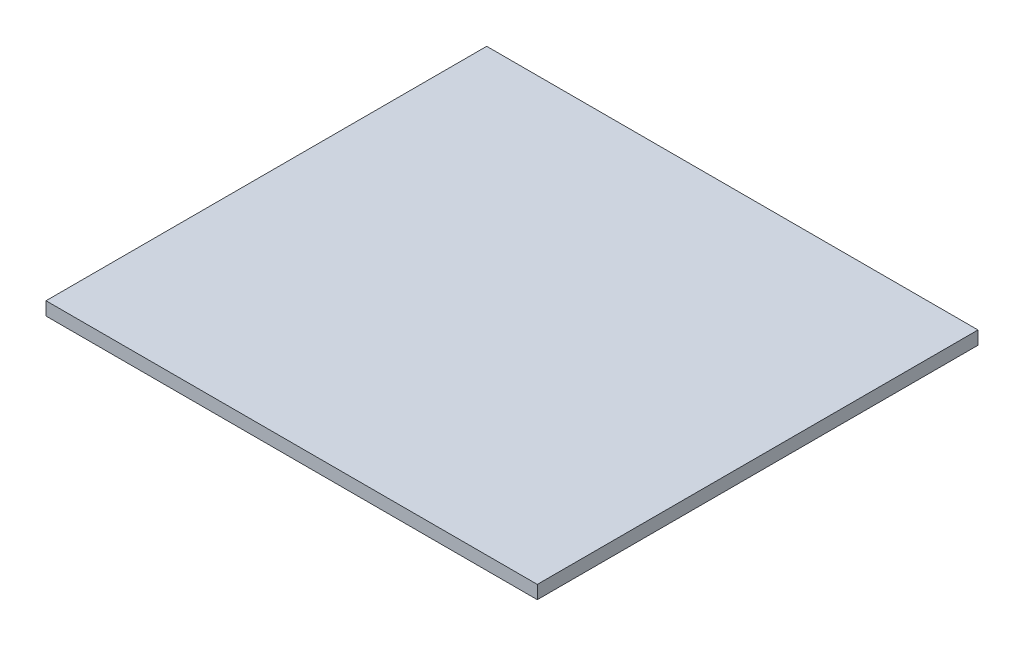
SolidWorks part; units mm, degrees
ref_plane "Front" through (0, 0, 0) normal (0, 0, 1) x (1, 0, 0)
ref_plane "Top" through (0, 0, 0) normal (0, 1, 0) x (1, 0, 0)
ref_plane "Right" through (0, 0, 0) normal (1, 0, 0) x (0, 0, -1)
sketch "Sketch1" plane through (0, 0, 0) normal (0, 1, 0) x (1, 0, 0)
  line L1 (235, -210.8) -> (-235, -210.8)
  line L2 (235, -210.8) -> (235, 210.8)
  line L3 (235, 210.8) -> (-235, 210.8)
  line L4 (-235, -210.8) -> (-235, 210.8)
  line L5 (235, -210.8) -> (-235, 210.8) construction
  line L6 (235, 210.8) -> (-235, -210.8) construction
  point P0 (0, 0)
  dimension "D1" = 470
  dimension "D2" = 421.6
extrude "Boss-Extrude1" add sketch "Sketch1" along normal blind 12.7
